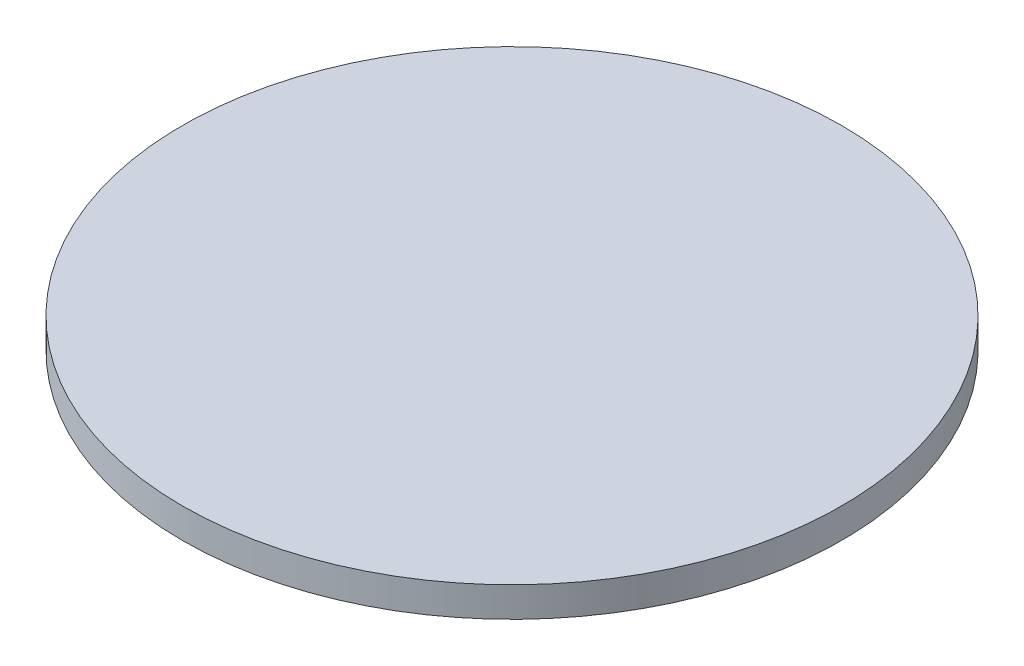
SolidWorks part; units mm, degrees
ref_plane "Front" through (0, 0, 0) normal (0, 0, 1) x (1, 0, 0)
ref_plane "Top" through (0, 0, 0) normal (0, 1, 0) x (1, 0, 0)
ref_plane "Right" through (0, 0, 0) normal (1, 0, 0) x (0, 0, -1)
sketch "Sketch1" plane through (0, 0, 0) normal (0, 1, 0) x (1, 0, 0)
  circle A0 centre (0, 0) radius 11
  dimension "D1" = 22
extrude "Boss-Extrude1" add sketch "Sketch1" along normal blind 1
sketch "Sketch2" plane through (0, 0, 0) normal (0, -1, 0) x (1, 0, 0)
  circle A0 centre (0, 0) radius 0.5
  dimension "D1" = 1
extrude "Boss-Extrude2" add sketch "Sketch2" along normal blind 2.5
